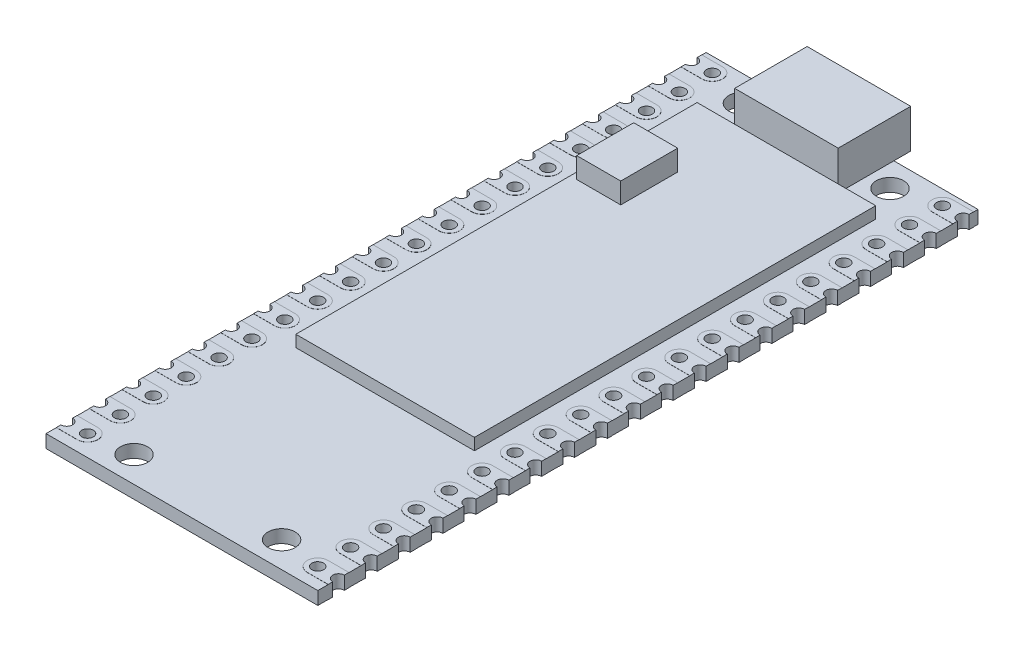
SolidWorks part; units mm, degrees
ref_plane "Front Plane" through (0, 0, 0) normal (0, 0, 1) x (1, 0, 0)
ref_plane "Top Plane" through (0, 0, 0) normal (0, 1, 0) x (1, 0, 0)
ref_plane "Right Plane" through (0, 0, 0) normal (1, 0, 0) x (0, 0, -1)
sketch "Sketch1" plane through (0, 0, 0) normal (0, 1, 0) x (1, 0, 0)
  line L0 (0, 0) -> (0, -51) construction
  line L1 (-10.5, 0) -> (10.5, 0)
  line L2 (-10.5, 0) -> (-10.5, -0.69)
  line L3 (-10.5, -51) -> (10.5, -51)
  line L4 (10.5, 0) -> (10.5, -0.69)
  line L5 (0, -25.5) -> (-10.5, -25.5) construction
  line L6 (-10.5, -48.95) -> (-8.89, -48.95) construction
  line L7 (-10.5, -49.85) -> (-10.5, -51)
  line L8 (10.5, -49.85) -> (10.5, -51)
  line L9 (-10.5, -47.31) -> (-10.5, -48.95)
  line L10 (-10.5, -44.77) -> (-10.5, -46.41)
  line L11 (-10.5, -42.23) -> (-10.5, -43.87)
  line L12 (-10.5, -39.69) -> (-10.5, -41.33)
  line L13 (-10.5, -37.15) -> (-10.5, -38.79)
  line L14 (-10.5, -34.61) -> (-10.5, -36.25)
  line L15 (-10.5, -32.07) -> (-10.5, -33.71)
  line L16 (-10.5, -29.53) -> (-10.5, -31.17)
  line L17 (-10.5, -26.99) -> (-10.5, -28.63)
  line L18 (-10.5, -24.45) -> (-10.5, -26.09)
  line L19 (-10.5, -21.91) -> (-10.5, -23.55)
  line L20 (-10.5, -19.37) -> (-10.5, -21.01)
  line L21 (-10.5, -16.83) -> (-10.5, -18.47)
  line L22 (-10.5, -14.29) -> (-10.5, -15.93)
  line L23 (-10.5, -11.75) -> (-10.5, -13.39)
  line L24 (-10.5, -9.21) -> (-10.5, -10.85)
  line L25 (-10.5, -6.67) -> (-10.5, -8.31)
  line L26 (-10.5, -4.13) -> (-10.5, -5.77)
  line L27 (-10.5, -1.59) -> (-10.5, -3.23)
  line L28 (10.5, -1.59) -> (10.5, -3.23)
  line L29 (10.5, -4.13) -> (10.5, -5.77)
  line L30 (10.5, -6.67) -> (10.5, -8.31)
  line L31 (10.5, -9.21) -> (10.5, -10.85)
  line L32 (10.5, -11.75) -> (10.5, -13.39)
  line L33 (10.5, -14.29) -> (10.5, -15.93)
  line L34 (10.5, -16.83) -> (10.5, -18.47)
  line L35 (10.5, -47.31) -> (10.5, -48.95)
  line L36 (10.5, -44.77) -> (10.5, -46.41)
  line L37 (10.5, -42.23) -> (10.5, -43.87)
  line L38 (10.5, -39.69) -> (10.5, -41.33)
  line L39 (10.5, -37.15) -> (10.5, -38.79)
  line L40 (10.5, -34.61) -> (10.5, -36.25)
  line L41 (10.5, -32.07) -> (10.5, -33.71)
  line L42 (10.5, -29.53) -> (10.5, -31.17)
  line L43 (10.5, -19.37) -> (10.5, -21.01)
  line L44 (10.5, -21.91) -> (10.5, -23.55)
  line L45 (10.5, -24.45) -> (10.5, -26.09)
  line L46 (10.5, -26.99) -> (10.5, -28.63)
  circle A0 centre (-5.7, -2) radius 1.05
  circle A1 centre (5.7, -2) radius 1.05
  circle A4 centre (-8.89, -49.4) radius 0.45
  arc A5 (-10.5, -49.85) -> (-10.5, -48.95) centre (-10.5, -49.4) ccw
  circle A6 centre (5.7, -49) radius 1.05
  circle A7 centre (-5.7, -49) radius 1.05
  arc A8 (10.5, -49.85) -> (10.5, -48.95) centre (10.5, -49.4) cw
  circle A9 centre (8.89, -49.4) radius 0.45
  arc A10 (-10.5, -47.31) -> (-10.5, -46.41) centre (-10.5, -46.86) ccw
  circle A11 centre (-8.89, -46.86) radius 0.45
  circle A12 centre (8.89, -46.86) radius 0.45
  arc A13 (10.5, -47.31) -> (10.5, -46.41) centre (10.5, -46.86) cw
  arc A14 (-10.5, -44.77) -> (-10.5, -43.87) centre (-10.5, -44.32) ccw
  circle A15 centre (-8.89, -44.32) radius 0.45
  circle A16 centre (8.89, -44.32) radius 0.45
  arc A17 (10.5, -44.77) -> (10.5, -43.87) centre (10.5, -44.32) cw
  arc A18 (-10.5, -42.23) -> (-10.5, -41.33) centre (-10.5, -41.78) ccw
  circle A19 centre (-8.89, -41.78) radius 0.45
  circle A20 centre (8.89, -41.78) radius 0.45
  arc A21 (10.5, -42.23) -> (10.5, -41.33) centre (10.5, -41.78) cw
  arc A22 (-10.5, -39.69) -> (-10.5, -38.79) centre (-10.5, -39.24) ccw
  circle A23 centre (-8.89, -39.24) radius 0.45
  circle A24 centre (8.89, -39.24) radius 0.45
  arc A25 (10.5, -39.69) -> (10.5, -38.79) centre (10.5, -39.24) cw
  arc A26 (-10.5, -37.15) -> (-10.5, -36.25) centre (-10.5, -36.7) ccw
  circle A27 centre (-8.89, -36.7) radius 0.45
  circle A28 centre (8.89, -36.7) radius 0.45
  arc A29 (10.5, -37.15) -> (10.5, -36.25) centre (10.5, -36.7) cw
  arc A30 (-10.5, -34.61) -> (-10.5, -33.71) centre (-10.5, -34.16) ccw
  circle A31 centre (-8.89, -34.16) radius 0.45
  circle A32 centre (8.89, -34.16) radius 0.45
  arc A33 (10.5, -34.61) -> (10.5, -33.71) centre (10.5, -34.16) cw
  arc A34 (-10.5, -32.07) -> (-10.5, -31.17) centre (-10.5, -31.62) ccw
  circle A35 centre (-8.89, -31.62) radius 0.45
  circle A36 centre (8.89, -31.62) radius 0.45
  arc A37 (10.5, -32.07) -> (10.5, -31.17) centre (10.5, -31.62) cw
  arc A38 (-10.5, -29.53) -> (-10.5, -28.63) centre (-10.5, -29.08) ccw
  circle A39 centre (-8.89, -29.08) radius 0.45
  circle A40 centre (8.89, -29.08) radius 0.45
  arc A41 (10.5, -29.53) -> (10.5, -28.63) centre (10.5, -29.08) cw
  arc A42 (-10.5, -26.99) -> (-10.5, -26.09) centre (-10.5, -26.54) ccw
  circle A43 centre (-8.89, -26.54) radius 0.45
  circle A44 centre (8.89, -26.54) radius 0.45
  arc A45 (10.5, -26.99) -> (10.5, -26.09) centre (10.5, -26.54) cw
  arc A46 (-10.5, -24.45) -> (-10.5, -23.55) centre (-10.5, -24) ccw
  circle A47 centre (-8.89, -24) radius 0.45
  circle A48 centre (8.89, -24) radius 0.45
  arc A49 (10.5, -24.45) -> (10.5, -23.55) centre (10.5, -24) cw
  arc A50 (-10.5, -21.91) -> (-10.5, -21.01) centre (-10.5, -21.46) ccw
  circle A51 centre (-8.89, -21.46) radius 0.45
  circle A52 centre (8.89, -21.46) radius 0.45
  arc A53 (10.5, -21.91) -> (10.5, -21.01) centre (10.5, -21.46) cw
  arc A54 (-10.5, -19.37) -> (-10.5, -18.47) centre (-10.5, -18.92) ccw
  circle A55 centre (-8.89, -18.92) radius 0.45
  circle A56 centre (8.89, -18.92) radius 0.45
  arc A57 (10.5, -19.37) -> (10.5, -18.47) centre (10.5, -18.92) cw
  arc A58 (-10.5, -16.83) -> (-10.5, -15.93) centre (-10.5, -16.38) ccw
  circle A59 centre (-8.89, -16.38) radius 0.45
  circle A60 centre (8.89, -16.38) radius 0.45
  arc A61 (10.5, -16.83) -> (10.5, -15.93) centre (10.5, -16.38) cw
  arc A62 (-10.5, -14.29) -> (-10.5, -13.39) centre (-10.5, -13.84) ccw
  circle A63 centre (-8.89, -13.84) radius 0.45
  circle A64 centre (8.89, -13.84) radius 0.45
  arc A65 (10.5, -14.29) -> (10.5, -13.39) centre (10.5, -13.84) cw
  arc A66 (-10.5, -11.75) -> (-10.5, -10.85) centre (-10.5, -11.3) ccw
  circle A67 centre (-8.89, -11.3) radius 0.45
  circle A68 centre (8.89, -11.3) radius 0.45
  arc A69 (10.5, -11.75) -> (10.5, -10.85) centre (10.5, -11.3) cw
  arc A70 (-10.5, -9.21) -> (-10.5, -8.31) centre (-10.5, -8.76) ccw
  circle A71 centre (-8.89, -8.76) radius 0.45
  circle A72 centre (8.89, -8.76) radius 0.45
  arc A73 (10.5, -9.21) -> (10.5, -8.31) centre (10.5, -8.76) cw
  arc A74 (-10.5, -6.67) -> (-10.5, -5.77) centre (-10.5, -6.22) ccw
  circle A75 centre (-8.89, -6.22) radius 0.45
  circle A76 centre (8.89, -6.22) radius 0.45
  arc A77 (10.5, -6.67) -> (10.5, -5.77) centre (10.5, -6.22) cw
  arc A78 (-10.5, -4.13) -> (-10.5, -3.23) centre (-10.5, -3.68) ccw
  circle A79 centre (-8.89, -3.68) radius 0.45
  circle A80 centre (8.89, -3.68) radius 0.45
  arc A81 (10.5, -4.13) -> (10.5, -3.23) centre (10.5, -3.68) cw
  arc A82 (-10.5, -1.59) -> (-10.5, -0.69) centre (-10.5, -1.14) ccw
  circle A83 centre (-8.89, -1.14) radius 0.45
  circle A84 centre (8.89, -1.14) radius 0.45
  arc A85 (10.5, -1.59) -> (10.5, -0.69) centre (10.5, -1.14) cw
other "Pen Sketch1" parameters "D3"=3.5614, "D8"=2.0664, "D1"=79.4088, "D2"=21, "D4"=15.5245, "D5"=11.4, "D6"=25.5, "D7"=1.5119, "D10"=2.54, "D9"=20
extrude "Boss-Extrude1" add sketch "Sketch1" along normal blind 1
sketch "Sketch2" plane through (0, 1, 0) normal (0, 1, 0) x (1, 0, 0)
  line L0 (0, -4.3) -> (0, 0) construction
  line L1 (-4, 1.3) -> (4, 1.3)
  line L2 (-4, 1.3) -> (-4, -4.3)
  line L3 (-4, -4.3) -> (4, -4.3)
  line L4 (4, 1.3) -> (4, -4.3)
  line L5 (10.5, 0) -> (-10.5, 0) construction
  dimension "D1" = 8
  dimension "D2" = 5.6
  dimension "D3" = 4.3
extrude "Boss-Extrude2" add sketch "Sketch2" along normal blind 3
sketch "Sketch3" plane through (0, 1, 0) normal (0, 1, 0) x (1, 0, 0)
  line L0 (-8.89, -48.6) -> (-10.5, -48.6)
  line L1 (-10.5, -47.31) -> (-10.5, -48.95) construction
  line L2 (-10.5, -48.6) -> (-10.5, -48.95)
  line L4 (-10.5, -49.85) -> (-10.5, -50.2)
  line L5 (-10.5, -49.85) -> (-10.5, -51) construction
  line L6 (-10.5, -50.2) -> (-8.89, -50.2)
  line L7 (0, 0) -> (0, -51) construction
  line L8 (-10.5, -51) -> (10.5, -51) construction
  line L9 (10.5, -50.2) -> (8.89, -50.2)
  line L10 (10.5, -49.85) -> (10.5, -50.2)
  line L11 (10.5, -48.6) -> (10.5, -48.95)
  line L12 (8.89, -48.6) -> (10.5, -48.6)
  line L13 (-8.89, -46.06) -> (-10.5, -46.06)
  line L14 (-10.5, -46.06) -> (-10.5, -46.41)
  line L15 (-10.5, -47.31) -> (-10.5, -47.66)
  line L16 (-10.5, -47.66) -> (-8.89, -47.66)
  line L17 (10.5, -47.66) -> (8.89, -47.66)
  line L18 (10.5, -47.31) -> (10.5, -47.66)
  line L19 (10.5, -46.06) -> (10.5, -46.41)
  line L20 (8.89, -46.06) -> (10.5, -46.06)
  line L21 (-8.89, -43.52) -> (-10.5, -43.52)
  line L22 (-10.5, -43.52) -> (-10.5, -43.87)
  line L23 (-10.5, -44.77) -> (-10.5, -45.12)
  line L24 (-10.5, -45.12) -> (-8.89, -45.12)
  line L25 (10.5, -45.12) -> (8.89, -45.12)
  line L26 (10.5, -44.77) -> (10.5, -45.12)
  line L27 (10.5, -43.52) -> (10.5, -43.87)
  line L28 (8.89, -43.52) -> (10.5, -43.52)
  line L29 (-8.89, -40.98) -> (-10.5, -40.98)
  line L30 (-10.5, -40.98) -> (-10.5, -41.33)
  line L31 (-10.5, -42.23) -> (-10.5, -42.58)
  line L32 (-10.5, -42.58) -> (-8.89, -42.58)
  line L33 (10.5, -42.58) -> (8.89, -42.58)
  line L34 (10.5, -42.23) -> (10.5, -42.58)
  line L35 (10.5, -40.98) -> (10.5, -41.33)
  line L36 (8.89, -40.98) -> (10.5, -40.98)
  line L37 (-8.89, -38.44) -> (-10.5, -38.44)
  line L38 (-10.5, -38.44) -> (-10.5, -38.79)
  line L39 (-10.5, -39.69) -> (-10.5, -40.04)
  line L40 (-10.5, -40.04) -> (-8.89, -40.04)
  line L41 (10.5, -40.04) -> (8.89, -40.04)
  line L42 (10.5, -39.69) -> (10.5, -40.04)
  line L43 (10.5, -38.44) -> (10.5, -38.79)
  line L44 (8.89, -38.44) -> (10.5, -38.44)
  line L45 (-8.89, -35.9) -> (-10.5, -35.9)
  line L46 (-10.5, -35.9) -> (-10.5, -36.25)
  line L47 (-10.5, -37.15) -> (-10.5, -37.5)
  line L48 (-10.5, -37.5) -> (-8.89, -37.5)
  line L49 (10.5, -37.5) -> (8.89, -37.5)
  line L50 (10.5, -37.15) -> (10.5, -37.5)
  line L51 (10.5, -35.9) -> (10.5, -36.25)
  line L52 (8.89, -35.9) -> (10.5, -35.9)
  line L53 (-8.89, -33.36) -> (-10.5, -33.36)
  line L54 (-10.5, -33.36) -> (-10.5, -33.71)
  line L55 (-10.5, -34.61) -> (-10.5, -34.96)
  line L56 (-10.5, -34.96) -> (-8.89, -34.96)
  line L57 (10.5, -34.96) -> (8.89, -34.96)
  line L58 (10.5, -34.61) -> (10.5, -34.96)
  line L59 (10.5, -33.36) -> (10.5, -33.71)
  line L60 (8.89, -33.36) -> (10.5, -33.36)
  line L61 (-8.89, -30.82) -> (-10.5, -30.82)
  line L62 (-10.5, -30.82) -> (-10.5, -31.17)
  line L63 (-10.5, -32.07) -> (-10.5, -32.42)
  line L64 (-10.5, -32.42) -> (-8.89, -32.42)
  line L65 (10.5, -32.42) -> (8.89, -32.42)
  line L66 (10.5, -32.07) -> (10.5, -32.42)
  line L67 (10.5, -30.82) -> (10.5, -31.17)
  line L68 (8.89, -30.82) -> (10.5, -30.82)
  line L69 (-8.89, -28.28) -> (-10.5, -28.28)
  line L70 (-10.5, -28.28) -> (-10.5, -28.63)
  line L71 (-10.5, -29.53) -> (-10.5, -29.88)
  line L72 (-10.5, -29.88) -> (-8.89, -29.88)
  line L73 (10.5, -29.88) -> (8.89, -29.88)
  line L74 (10.5, -29.53) -> (10.5, -29.88)
  line L75 (10.5, -28.28) -> (10.5, -28.63)
  line L76 (8.89, -28.28) -> (10.5, -28.28)
  line L77 (-8.89, -25.74) -> (-10.5, -25.74)
  line L78 (-10.5, -25.74) -> (-10.5, -26.09)
  line L79 (-10.5, -26.99) -> (-10.5, -27.34)
  line L80 (-10.5, -27.34) -> (-8.89, -27.34)
  line L81 (10.5, -27.34) -> (8.89, -27.34)
  line L82 (10.5, -26.99) -> (10.5, -27.34)
  line L83 (10.5, -25.74) -> (10.5, -26.09)
  line L84 (8.89, -25.74) -> (10.5, -25.74)
  line L85 (-8.89, -23.2) -> (-10.5, -23.2)
  line L86 (-10.5, -23.2) -> (-10.5, -23.55)
  line L87 (-10.5, -24.45) -> (-10.5, -24.8)
  line L88 (-10.5, -24.8) -> (-8.89, -24.8)
  line L89 (10.5, -24.8) -> (8.89, -24.8)
  line L90 (10.5, -24.45) -> (10.5, -24.8)
  line L91 (10.5, -23.2) -> (10.5, -23.55)
  line L92 (8.89, -23.2) -> (10.5, -23.2)
  line L93 (-8.89, -20.66) -> (-10.5, -20.66)
  line L94 (-10.5, -20.66) -> (-10.5, -21.01)
  line L95 (-10.5, -21.91) -> (-10.5, -22.26)
  line L96 (-10.5, -22.26) -> (-8.89, -22.26)
  line L97 (10.5, -22.26) -> (8.89, -22.26)
  line L98 (10.5, -21.91) -> (10.5, -22.26)
  line L99 (10.5, -20.66) -> (10.5, -21.01)
  line L100 (8.89, -20.66) -> (10.5, -20.66)
  line L101 (-8.89, -18.12) -> (-10.5, -18.12)
  line L102 (-10.5, -18.12) -> (-10.5, -18.47)
  line L103 (-10.5, -19.37) -> (-10.5, -19.72)
  line L104 (-10.5, -19.72) -> (-8.89, -19.72)
  line L105 (10.5, -19.72) -> (8.89, -19.72)
  line L106 (10.5, -19.37) -> (10.5, -19.72)
  line L107 (10.5, -18.12) -> (10.5, -18.47)
  line L108 (8.89, -18.12) -> (10.5, -18.12)
  line L109 (-8.89, -15.58) -> (-10.5, -15.58)
  line L110 (-10.5, -15.58) -> (-10.5, -15.93)
  line L111 (-10.5, -16.83) -> (-10.5, -17.18)
  line L112 (-10.5, -17.18) -> (-8.89, -17.18)
  line L113 (10.5, -17.18) -> (8.89, -17.18)
  line L114 (10.5, -16.83) -> (10.5, -17.18)
  line L115 (10.5, -15.58) -> (10.5, -15.93)
  line L116 (8.89, -15.58) -> (10.5, -15.58)
  line L117 (-8.89, -13.04) -> (-10.5, -13.04)
  line L118 (-10.5, -13.04) -> (-10.5, -13.39)
  line L119 (-10.5, -14.29) -> (-10.5, -14.64)
  line L120 (-10.5, -14.64) -> (-8.89, -14.64)
  line L121 (10.5, -14.64) -> (8.89, -14.64)
  line L122 (10.5, -14.29) -> (10.5, -14.64)
  line L123 (10.5, -13.04) -> (10.5, -13.39)
  line L124 (8.89, -13.04) -> (10.5, -13.04)
  line L125 (-8.89, -10.5) -> (-10.5, -10.5)
  line L126 (-10.5, -10.5) -> (-10.5, -10.85)
  line L127 (-10.5, -11.75) -> (-10.5, -12.1)
  line L128 (-10.5, -12.1) -> (-8.89, -12.1)
  line L129 (10.5, -12.1) -> (8.89, -12.1)
  line L130 (10.5, -11.75) -> (10.5, -12.1)
  line L131 (10.5, -10.5) -> (10.5, -10.85)
  line L132 (8.89, -10.5) -> (10.5, -10.5)
  line L133 (-8.89, -7.96) -> (-10.5, -7.96)
  line L134 (-10.5, -7.96) -> (-10.5, -8.31)
  line L135 (-10.5, -9.21) -> (-10.5, -9.56)
  line L136 (-10.5, -9.56) -> (-8.89, -9.56)
  line L137 (10.5, -9.56) -> (8.89, -9.56)
  line L138 (10.5, -9.21) -> (10.5, -9.56)
  line L139 (10.5, -7.96) -> (10.5, -8.31)
  line L140 (8.89, -7.96) -> (10.5, -7.96)
  line L141 (-8.89, -5.42) -> (-10.5, -5.42)
  line L142 (-10.5, -5.42) -> (-10.5, -5.77)
  line L143 (-10.5, -6.67) -> (-10.5, -7.02)
  line L144 (-10.5, -7.02) -> (-8.89, -7.02)
  line L145 (10.5, -7.02) -> (8.89, -7.02)
  line L146 (10.5, -6.67) -> (10.5, -7.02)
  line L147 (10.5, -5.42) -> (10.5, -5.77)
  line L148 (8.89, -5.42) -> (10.5, -5.42)
  line L149 (-8.89, -2.88) -> (-10.5, -2.88)
  line L150 (-10.5, -2.88) -> (-10.5, -3.23)
  line L151 (-10.5, -4.13) -> (-10.5, -4.48)
  line L152 (-10.5, -4.48) -> (-8.89, -4.48)
  line L153 (10.5, -4.48) -> (8.89, -4.48)
  line L154 (10.5, -4.13) -> (10.5, -4.48)
  line L155 (10.5, -2.88) -> (10.5, -3.23)
  line L156 (8.89, -2.88) -> (10.5, -2.88)
  line L157 (-8.89, -0.34) -> (-10.5, -0.34)
  line L158 (-10.5, -0.34) -> (-10.5, -0.69)
  line L159 (-10.5, -1.59) -> (-10.5, -1.94)
  line L160 (-10.5, -1.94) -> (-8.89, -1.94)
  line L161 (10.5, -1.94) -> (8.89, -1.94)
  line L162 (10.5, -1.59) -> (10.5, -1.94)
  line L163 (10.5, -0.34) -> (10.5, -0.69)
  line L164 (8.89, -0.34) -> (10.5, -0.34)
  arc A0 (-8.89, -50.2) -> (-8.89, -48.6) centre (-8.89, -49.4) ccw
  arc A1 (-10.5, -49.85) -> (-10.5, -48.95) centre (-10.5, -49.4) ccw
  circle A2 centre (-8.89, -49.4) radius 0.45
  circle A3 centre (-8.89, -49.4) radius 0.45 construction
  arc A4 (-10.5, -49.85) -> (-10.5, -48.95) centre (-10.5, -49.4) ccw construction
  circle A5 centre (8.89, -49.4) radius 0.45
  arc A6 (10.5, -49.85) -> (10.5, -48.95) centre (10.5, -49.4) cw
  arc A7 (8.89, -50.2) -> (8.89, -48.6) centre (8.89, -49.4) cw
  arc A8 (-8.89, -47.66) -> (-8.89, -46.06) centre (-8.89, -46.86) ccw
  arc A9 (-10.5, -47.31) -> (-10.5, -46.41) centre (-10.5, -46.86) ccw
  circle A10 centre (-8.89, -46.86) radius 0.45
  circle A11 centre (8.89, -46.86) radius 0.45
  arc A12 (10.5, -47.31) -> (10.5, -46.41) centre (10.5, -46.86) cw
  arc A13 (8.89, -47.66) -> (8.89, -46.06) centre (8.89, -46.86) cw
  arc A14 (-8.89, -45.12) -> (-8.89, -43.52) centre (-8.89, -44.32) ccw
  arc A15 (-10.5, -44.77) -> (-10.5, -43.87) centre (-10.5, -44.32) ccw
  circle A16 centre (-8.89, -44.32) radius 0.45
  circle A17 centre (8.89, -44.32) radius 0.45
  arc A18 (10.5, -44.77) -> (10.5, -43.87) centre (10.5, -44.32) cw
  arc A19 (8.89, -45.12) -> (8.89, -43.52) centre (8.89, -44.32) cw
  arc A20 (-8.89, -42.58) -> (-8.89, -40.98) centre (-8.89, -41.78) ccw
  arc A21 (-10.5, -42.23) -> (-10.5, -41.33) centre (-10.5, -41.78) ccw
  circle A22 centre (-8.89, -41.78) radius 0.45
  circle A23 centre (8.89, -41.78) radius 0.45
  arc A24 (10.5, -42.23) -> (10.5, -41.33) centre (10.5, -41.78) cw
  arc A25 (8.89, -42.58) -> (8.89, -40.98) centre (8.89, -41.78) cw
  arc A26 (-8.89, -40.04) -> (-8.89, -38.44) centre (-8.89, -39.24) ccw
  arc A27 (-10.5, -39.69) -> (-10.5, -38.79) centre (-10.5, -39.24) ccw
  circle A28 centre (-8.89, -39.24) radius 0.45
  circle A29 centre (8.89, -39.24) radius 0.45
  arc A30 (10.5, -39.69) -> (10.5, -38.79) centre (10.5, -39.24) cw
  arc A31 (8.89, -40.04) -> (8.89, -38.44) centre (8.89, -39.24) cw
  arc A32 (-8.89, -37.5) -> (-8.89, -35.9) centre (-8.89, -36.7) ccw
  arc A33 (-10.5, -37.15) -> (-10.5, -36.25) centre (-10.5, -36.7) ccw
  circle A34 centre (-8.89, -36.7) radius 0.45
  circle A35 centre (8.89, -36.7) radius 0.45
  arc A36 (10.5, -37.15) -> (10.5, -36.25) centre (10.5, -36.7) cw
  arc A37 (8.89, -37.5) -> (8.89, -35.9) centre (8.89, -36.7) cw
  arc A38 (-8.89, -34.96) -> (-8.89, -33.36) centre (-8.89, -34.16) ccw
  arc A39 (-10.5, -34.61) -> (-10.5, -33.71) centre (-10.5, -34.16) ccw
  circle A40 centre (-8.89, -34.16) radius 0.45
  circle A41 centre (8.89, -34.16) radius 0.45
  arc A42 (10.5, -34.61) -> (10.5, -33.71) centre (10.5, -34.16) cw
  arc A43 (8.89, -34.96) -> (8.89, -33.36) centre (8.89, -34.16) cw
  arc A44 (-8.89, -32.42) -> (-8.89, -30.82) centre (-8.89, -31.62) ccw
  arc A45 (-10.5, -32.07) -> (-10.5, -31.17) centre (-10.5, -31.62) ccw
  circle A46 centre (-8.89, -31.62) radius 0.45
  circle A47 centre (8.89, -31.62) radius 0.45
  arc A48 (10.5, -32.07) -> (10.5, -31.17) centre (10.5, -31.62) cw
  arc A49 (8.89, -32.42) -> (8.89, -30.82) centre (8.89, -31.62) cw
  arc A50 (-8.89, -29.88) -> (-8.89, -28.28) centre (-8.89, -29.08) ccw
  arc A51 (-10.5, -29.53) -> (-10.5, -28.63) centre (-10.5, -29.08) ccw
  circle A52 centre (-8.89, -29.08) radius 0.45
  circle A53 centre (8.89, -29.08) radius 0.45
  arc A54 (10.5, -29.53) -> (10.5, -28.63) centre (10.5, -29.08) cw
  arc A55 (8.89, -29.88) -> (8.89, -28.28) centre (8.89, -29.08) cw
  arc A56 (-8.89, -27.34) -> (-8.89, -25.74) centre (-8.89, -26.54) ccw
  arc A57 (-10.5, -26.99) -> (-10.5, -26.09) centre (-10.5, -26.54) ccw
  circle A58 centre (-8.89, -26.54) radius 0.45
  circle A59 centre (8.89, -26.54) radius 0.45
  arc A60 (10.5, -26.99) -> (10.5, -26.09) centre (10.5, -26.54) cw
  arc A61 (8.89, -27.34) -> (8.89, -25.74) centre (8.89, -26.54) cw
  arc A62 (-8.89, -24.8) -> (-8.89, -23.2) centre (-8.89, -24) ccw
  arc A63 (-10.5, -24.45) -> (-10.5, -23.55) centre (-10.5, -24) ccw
  circle A64 centre (-8.89, -24) radius 0.45
  circle A65 centre (8.89, -24) radius 0.45
  arc A66 (10.5, -24.45) -> (10.5, -23.55) centre (10.5, -24) cw
  arc A67 (8.89, -24.8) -> (8.89, -23.2) centre (8.89, -24) cw
  arc A68 (-8.89, -22.26) -> (-8.89, -20.66) centre (-8.89, -21.46) ccw
  arc A69 (-10.5, -21.91) -> (-10.5, -21.01) centre (-10.5, -21.46) ccw
  circle A70 centre (-8.89, -21.46) radius 0.45
  circle A71 centre (8.89, -21.46) radius 0.45
  arc A72 (10.5, -21.91) -> (10.5, -21.01) centre (10.5, -21.46) cw
  arc A73 (8.89, -22.26) -> (8.89, -20.66) centre (8.89, -21.46) cw
  arc A74 (-8.89, -19.72) -> (-8.89, -18.12) centre (-8.89, -18.92) ccw
  arc A75 (-10.5, -19.37) -> (-10.5, -18.47) centre (-10.5, -18.92) ccw
  circle A76 centre (-8.89, -18.92) radius 0.45
  circle A77 centre (8.89, -18.92) radius 0.45
  arc A78 (10.5, -19.37) -> (10.5, -18.47) centre (10.5, -18.92) cw
  arc A79 (8.89, -19.72) -> (8.89, -18.12) centre (8.89, -18.92) cw
  arc A80 (-8.89, -17.18) -> (-8.89, -15.58) centre (-8.89, -16.38) ccw
  arc A81 (-10.5, -16.83) -> (-10.5, -15.93) centre (-10.5, -16.38) ccw
  circle A82 centre (-8.89, -16.38) radius 0.45
  circle A83 centre (8.89, -16.38) radius 0.45
  arc A84 (10.5, -16.83) -> (10.5, -15.93) centre (10.5, -16.38) cw
  arc A85 (8.89, -17.18) -> (8.89, -15.58) centre (8.89, -16.38) cw
  arc A86 (-8.89, -14.64) -> (-8.89, -13.04) centre (-8.89, -13.84) ccw
  arc A87 (-10.5, -14.29) -> (-10.5, -13.39) centre (-10.5, -13.84) ccw
  circle A88 centre (-8.89, -13.84) radius 0.45
  circle A89 centre (8.89, -13.84) radius 0.45
  arc A90 (10.5, -14.29) -> (10.5, -13.39) centre (10.5, -13.84) cw
  arc A91 (8.89, -14.64) -> (8.89, -13.04) centre (8.89, -13.84) cw
  arc A92 (-8.89, -12.1) -> (-8.89, -10.5) centre (-8.89, -11.3) ccw
  arc A93 (-10.5, -11.75) -> (-10.5, -10.85) centre (-10.5, -11.3) ccw
  circle A94 centre (-8.89, -11.3) radius 0.45
  circle A95 centre (8.89, -11.3) radius 0.45
  arc A96 (10.5, -11.75) -> (10.5, -10.85) centre (10.5, -11.3) cw
  arc A97 (8.89, -12.1) -> (8.89, -10.5) centre (8.89, -11.3) cw
  arc A98 (-8.89, -9.56) -> (-8.89, -7.96) centre (-8.89, -8.76) ccw
  arc A99 (-10.5, -9.21) -> (-10.5, -8.31) centre (-10.5, -8.76) ccw
  circle A100 centre (-8.89, -8.76) radius 0.45
  circle A101 centre (8.89, -8.76) radius 0.45
  arc A102 (10.5, -9.21) -> (10.5, -8.31) centre (10.5, -8.76) cw
  arc A103 (8.89, -9.56) -> (8.89, -7.96) centre (8.89, -8.76) cw
  arc A104 (-8.89, -7.02) -> (-8.89, -5.42) centre (-8.89, -6.22) ccw
  arc A105 (-10.5, -6.67) -> (-10.5, -5.77) centre (-10.5, -6.22) ccw
  circle A106 centre (-8.89, -6.22) radius 0.45
  circle A107 centre (8.89, -6.22) radius 0.45
  arc A108 (10.5, -6.67) -> (10.5, -5.77) centre (10.5, -6.22) cw
  arc A109 (8.89, -7.02) -> (8.89, -5.42) centre (8.89, -6.22) cw
  arc A110 (-8.89, -4.48) -> (-8.89, -2.88) centre (-8.89, -3.68) ccw
  arc A111 (-10.5, -4.13) -> (-10.5, -3.23) centre (-10.5, -3.68) ccw
  circle A112 centre (-8.89, -3.68) radius 0.45
  circle A113 centre (8.89, -3.68) radius 0.45
  arc A114 (10.5, -4.13) -> (10.5, -3.23) centre (10.5, -3.68) cw
  arc A115 (8.89, -4.48) -> (8.89, -2.88) centre (8.89, -3.68) cw
  arc A116 (-8.89, -1.94) -> (-8.89, -0.34) centre (-8.89, -1.14) ccw
  arc A117 (-10.5, -1.59) -> (-10.5, -0.69) centre (-10.5, -1.14) ccw
  circle A118 centre (-8.89, -1.14) radius 0.45
  circle A119 centre (8.89, -1.14) radius 0.45
  arc A120 (10.5, -1.59) -> (10.5, -0.69) centre (10.5, -1.14) cw
  arc A121 (8.89, -1.94) -> (8.89, -0.34) centre (8.89, -1.14) cw
  circle A122 centre (-8.89, -1.14) radius 0.45 construction
  dimension "D1" = 1.6
  dimension "D2" = 20
extrude "Boss-Extrude3" add sketch "Sketch3" along normal blind 0.01 and the other way blind 1.01
sketch "Sketch4" plane through (0, 1, 0) normal (0, 1, 0) x (1, 0, 0)
  line L0 (-10.5, -27.34) -> (-10.5, -28.28) construction
  line L1 (-3.5, -22.3) -> (3.5, -22.3) construction
  line L2 (-3.5, -22.3) -> (-3.5, -29.3) construction
  line L3 (-3.5, -29.3) -> (3.5, -29.3) construction
  line L4 (3.5, -22.3) -> (3.5, -29.3) construction
  line L5 (-10.5, -51) -> (10.5, -51) construction
  line L6 (-6.6, -35.6) -> (7.2, -35.6)
  line L9 (7.2, -35.6) -> (7.2, -4.6)
  line L10 (7.2, -4.6) -> (-6.6, -4.6)
  line L11 (-6.6, -4.6) -> (-6.6, -35.6)
  line L14 (-10.5, -19.72) -> (-10.5, -20.66) construction
  line L16 (10.5, -18.12) -> (10.5, -17.18) construction
  line L17 (10.5, 0) -> (4, 0) construction
  dimension "D1" = 7
  dimension "D2" = 7
  dimension "D3" = 7
  dimension "D4" = 21.7
  dimension "D5" = 3.9
  dimension "D7" = 3.3
  dimension "D8" = 4.6
  dimension "D10" = 15.4
extrude "Boss-Extrude4" add sketch "Sketch4" along normal blind 0.9
sketch "Sketch5" plane through (0, 1, 0) normal (0, 1, 0) x (1, 0, 0)
  line L0 (-10.5, -14.64) -> (-10.5, -15.58) construction
  line L1 (-6.1, -10) -> (-2.7, -10)
  line L2 (-6.1, -10) -> (-6.1, -14.4)
  line L3 (-6.1, -14.4) -> (-2.7, -14.4)
  line L4 (-2.7, -10) -> (-2.7, -14.4)
  line L5 (-4, 0) -> (-10.5, 0) construction
  dimension "D1" = 3.4
  dimension "D2" = 4.4
  dimension "D3" = 4.4
  dimension "D4" = 10
extrude "Boss-Extrude5" add sketch "Sketch5" along normal blind 2.5
